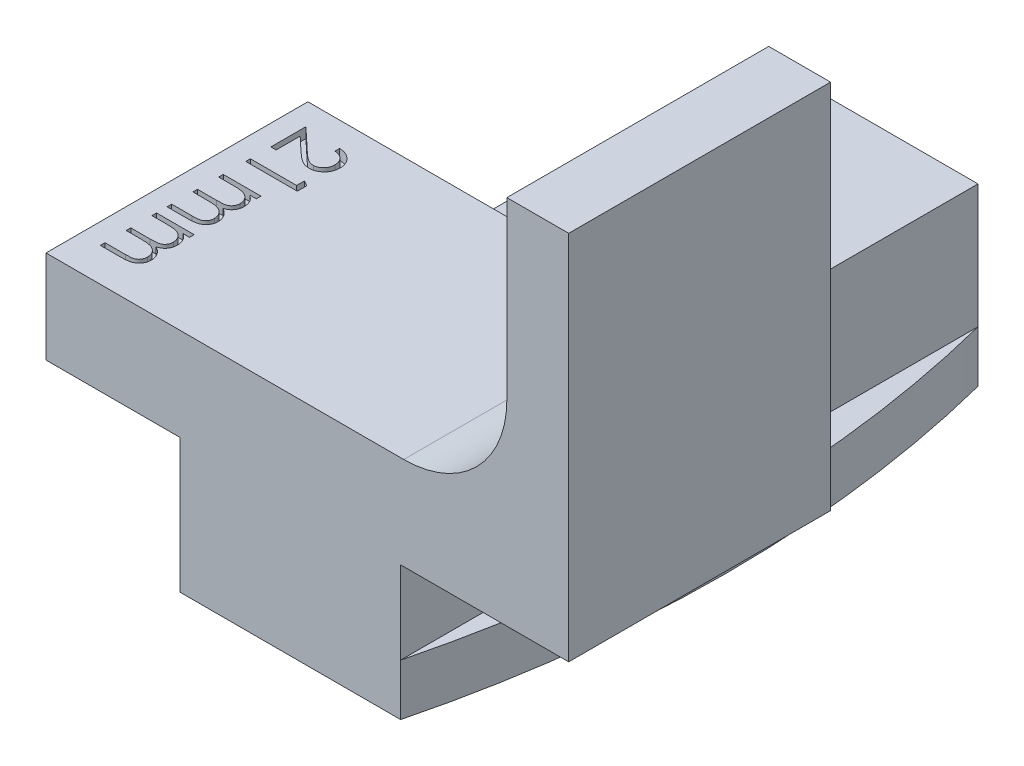
SolidWorks part; units mm, degrees
ref_plane "Front Plane" through (0, 0, 0) normal (0, 0, 1) x (1, 0, 0)
ref_plane "Top Plane" through (0, 0, 0) normal (0, 1, 0) x (1, 0, 0)
ref_plane "Right Plane" through (0, 0, 0) normal (1, 0, 0) x (0, 0, -1)
sketch "Sketch1" plane through (0, 0, 0) normal (0, 0, 1) x (1, 0, 0)
  line L0 (0, 0) -> (0, -4)
  line L1 (0, -4) -> (-1.75, -4)
  line L2 (-1.75, -4) -> (-1.75, -6.5)
  line L8 (12.45, -6.5) -> (12.45, -4)
  line L9 (12.45, -4) -> (10.7, -4)
  line L10 (10.7, -4) -> (10.7, 0)
  line L11 (10.7, 0) -> (18.85, 0)
  line L12 (18.85, 0) -> (18.85, 18)
  line L13 (18.85, 18) -> (15.85, 18)
  line L14 (15.85, 18) -> (15.85, 4.5)
  line L15 (15.85, 4.5) -> (-6.5, 4.5)
  line L16 (-6.5, 4.5) -> (-6.5, 0)
  line L17 (-6.5, 0) -> (0, 0)
  line L18 (5.35, -6.5) -> (5.35, 15) construction
  line L19 (-1.75, -6.5) -> (12.45, -6.5)
  circle A0 centre (5.35, 15) radius 10.5 construction
  point P3 (5.35, -6.5)
  dimension "D9" = 15
  dimension "D8" = 21
  dimension "D2" = 2.5
  dimension "D3" = 10.7
  dimension "D4" = 4
  dimension "D5" = 14.2
  dimension "D6" = 3
  dimension "D7" = 3
  dimension "D10" = 6.5
extrude "Boss-Extrude1" add sketch "Sketch1" along normal blind 12.7
fillet "Fillet1" radius 5 1 edges at (15.85, 4.5, 6.35)
sketch "Sketch3" plane through (0, 0, 12.7) normal (0, 0, 1) x (1, 0, 0)
  line L0 (0, 0) -> (0, 2)
  line L1 (0, 2) -> (10.7, 2)
  line L2 (10.7, 2) -> (10.7, 0)
  line L14 (-6.5, 0) -> (0, 0)
  line L15 (0, 0) -> (0, -4)
  line L16 (0, -4) -> (-1.75, -4)
  line L17 (-1.75, -4) -> (-1.75, -6.5)
  line L18 (-1.75, -6.5) -> (12.45, -6.5)
  line L19 (12.45, -6.5) -> (12.45, -4)
  line L20 (12.45, -4) -> (10.7, -4)
  line L21 (10.7, -4) -> (10.7, 0)
  line L22 (10.7, 0) -> (18.85, 0)
  line L23 (18.85, 0) -> (18.85, 18)
  line L24 (18.85, 18) -> (15.85, 18)
  line L25 (15.85, 18) -> (15.85, 9.5)
  line L26 (10.85, 4.5) -> (-6.5, 4.5)
  line L27 (-6.5, 4.5) -> (-6.5, 0)
  line L29 (0, 0) -> (0, -4)
  line L30 (0, -4) -> (-1.75, -4)
  line L31 (-1.75, -4) -> (-1.75, -6.5)
  line L32 (-1.75, -6.5) -> (12.45, -6.5)
  line L33 (12.45, -6.5) -> (12.45, -4)
  line L34 (12.45, -4) -> (10.7, -4)
  line L35 (10.7, -4) -> (10.7, 0)
  arc A1 (10.85, 4.5) -> (15.85, 9.5) centre (10.85, 9.5) ccw
  dimension "D2" = 2
  dimension "D1" = 0
extrude "Boss-Extrude2" add sketch "Sketch3" against normal blind 28
sketch "Sketch2" plane through (0, -4, 0) normal (0, 1, 0) x (1, 0, 0)
  line L0 (0, 15.3) -> (10.7, 15.3)
  line L1 (10.7, -12.7) -> (0, -12.7)
  line L4 (-1.75, -12.7) -> (-1.75, 15.3) construction
  line L5 (12.45, -12.7) -> (12.45, 15.3) construction
  arc A2 (0, 15.3) -> (0, -12.7) centre (55.125, 1.3) ccw
  arc A3 (10.7, -12.7) -> (10.7, 15.3) centre (-44.425, 1.3) ccw
extrude "Cut-Extrude1" cut sketch "Sketch2" against normal blind 10 flip side to cut
sketch "Sketch4" plane through (0, 4.5, 0) normal (0, 1, 0) x (1, 0, 0)
  line L0 (-5.5, -1) -> (-5.5, -12.1308) construction
  line L1 (10.85, 0) -> (-6.5, 0) construction
  line L2 (-6.5, -12.7) -> (-6.5, 0) construction
  text T0 "21mm" font "Century Gothic" height 2.5
  point P7 (-5.5, -12.1308)
  dimension "D1" = 1
  dimension "D2" = 1
extrude "Cut-Extrude2" cut sketch "Sketch4" against normal blind 0.5
